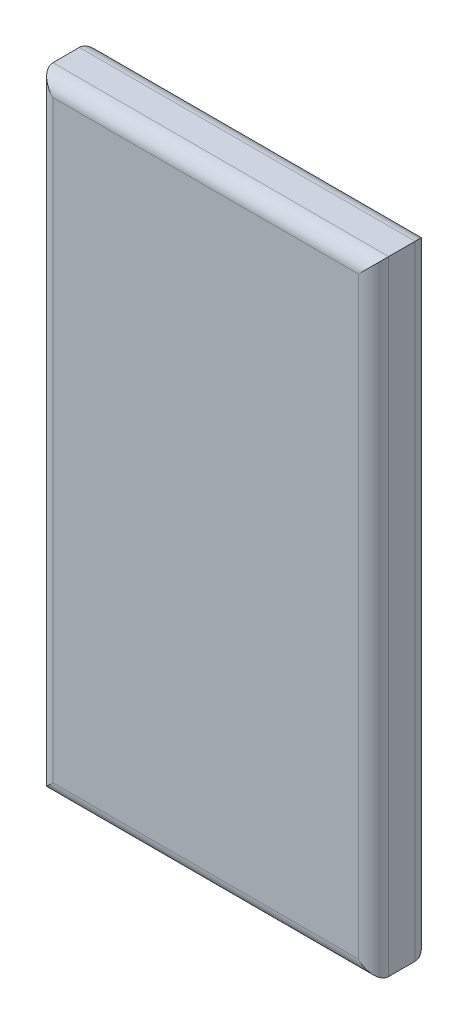
SolidWorks part; units mm, degrees
ref_plane "Front Plane" through (0, 0, 0) normal (0, 0, 1) x (1, 0, 0)
ref_plane "Top Plane" through (0, 0, 0) normal (0, 1, 0) x (1, 0, 0)
ref_plane "Right Plane" through (0, 0, 0) normal (1, 0, 0) x (0, 0, -1)
sketch "Sketch1" plane through (0, 0, 0) normal (0, 0, 1) x (1, 0, 0)
  line L1 (0, 33.02) -> (17.78, 33.02)
  line L2 (0, 33.02) -> (0, 0)
  line L3 (0, 0) -> (17.78, 0)
  line L4 (17.78, 33.02) -> (17.78, 0)
  dimension "D1" = 17.78
  dimension "D2" = 33.02
  dimension "D3" = 0
extrude "Boss-Extrude1" add sketch "Sketch1" along normal blind 3
fillet "Fillet2" radius 0.8 8 edges at (8.89, 0, 0) (8.89, 0, 3) (8.89, 33.02, 0) (8.89, 33.02, 3) (17.78, 16.51, 3) (17.78, 16.51, 0) (0, 16.51, 0) (0, 16.51, 3)
